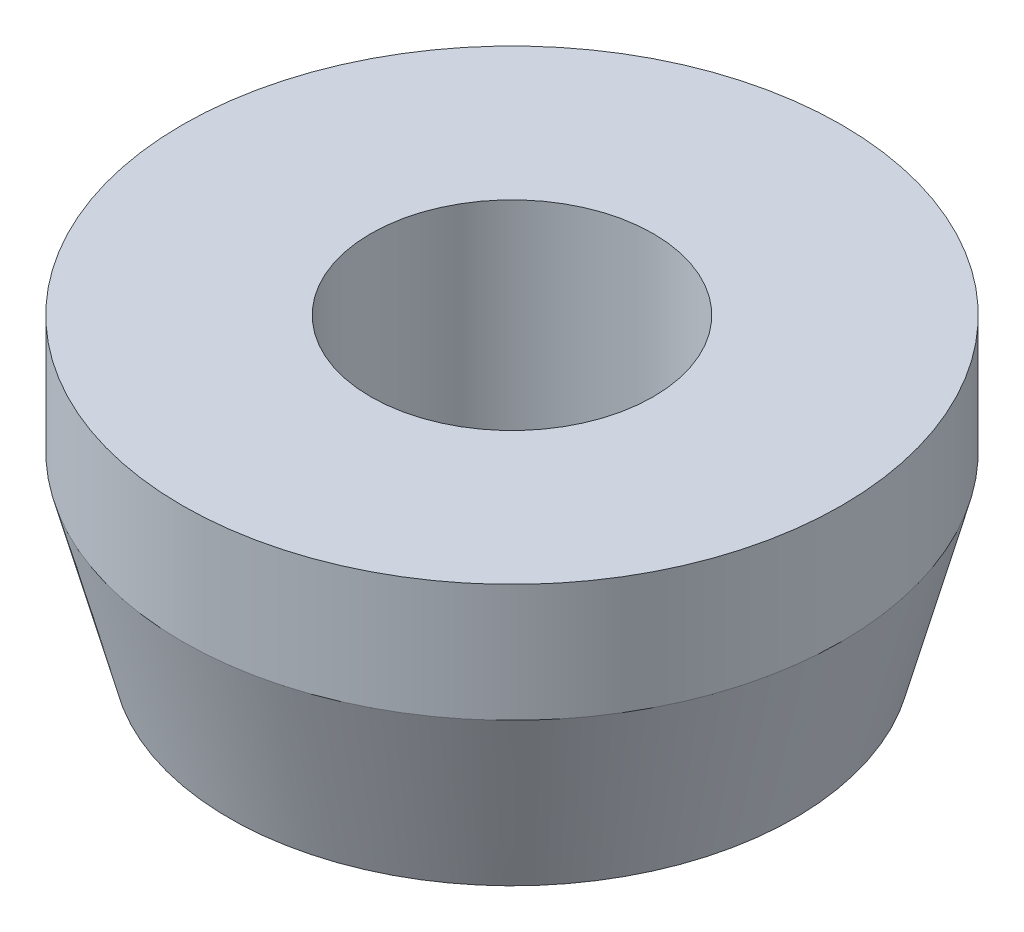
SolidWorks part; units mm, degrees
material "SANTOPRENE"
ref_plane "Front Plane" through (0, 0, 0) normal (0, 0, 1) x (1, 0, 0)
ref_plane "Top Plane" through (0, 0, 0) normal (0, 1, 0) x (1, 0, 0)
ref_plane "Right Plane" through (0, 0, 0) normal (1, 0, 0) x (0, 0, -1)
sketch "Sketch1" plane through (0, 0, 0) normal (0, 0, 1) x (1, 0, 0)
  line L0 (0, 0) -> (0, 24.4129) construction
  line L1 (3.556, 1.905) -> (3.048, 0)
  line L2 (1.524, 3.175) -> (3.048, 3.175)
  line L3 (1.524, 3.175) -> (1.524, 0)
  line L4 (1.524, 0) -> (3.048, 0)
  line L6 (3.048, 3.175) -> (3.556, 3.175)
  line L9 (3.556, 3.175) -> (3.556, 1.905)
  dimension "D1" = 0
  dimension "D2" = 1.524
  dimension "D3" = 1.524
  dimension "D4" = 3.175
  dimension "D5" = 2.032
  dimension "D6" = 1.27
  dimension "D7" = 1.524
revolve "Revolve1" add sketch "Sketch1" angle 360 about L0
